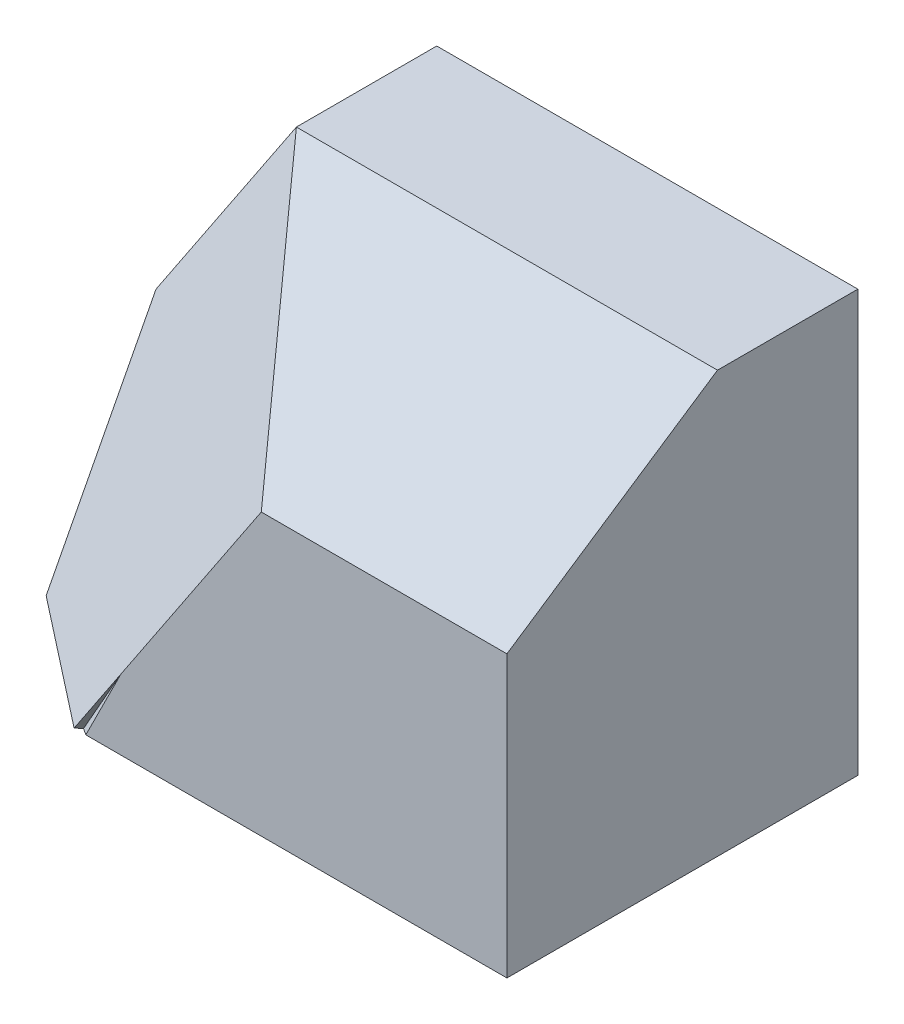
SolidWorks part; units mm, degrees
ref_plane "Front Plane" through (0, 0, 0) normal (0, 0, 1) x (1, 0, 0)
ref_plane "Top Plane" through (0, 0, 0) normal (0, 1, 0) x (1, 0, 0)
ref_plane "Right Plane" through (0, 0, 0) normal (1, 0, 0) x (0, 0, -1)
sketch "Sketch1" plane through (0, 0, 0) normal (0, 0, 1) x (1, 0, 0)
  line L1 (0, 0) -> (80, 0)
  line L2 (0, 0) -> (0, 60)
  line L3 (0, 60) -> (80, 60)
  line L4 (80, 0) -> (80, 60)
  dimension "D1" = 80
  dimension "D2" = 60
extrude "Boss-Extrude1" add sketch "Sketch1" along normal blind 50
sketch "Sketch2" plane through (0, 0, 50) normal (0, 0, 1) x (1, 0, 0)
  line L0 (0, 30) -> (20, 60)
  line L1 (0, 60) -> (0, 0) construction
  line L2 (80, 60) -> (0, 60) construction
  line L3 (20, 60) -> (0, 60)
  line L4 (0, 60) -> (0, 30)
  dimension "D1" = 20
  dimension "D2" = 30
extrude "Cut-Extrude1" cut sketch "Sketch2" against normal blind 50
sketch "Sketch3" plane through (80, 0, 0) normal (1, 0, 0) x (0, 0, -1)
  line L0 (-30, 60) -> (-50, 40)
  line L1 (-50, 60) -> (0, 60) construction
  line L2 (-50, 0) -> (-50, 60) construction
  line L3 (-50, 40) -> (-50, 60)
  line L4 (-50, 60) -> (-30, 60)
  dimension "D1" = 20
  dimension "D2" = 20
extrude "Cut-Extrude2" cut sketch "Sketch3" against normal blind 124
sketch "Sketch4" plane through (0, 0, 50) normal (0, 0, 1) x (1, 0, 0)
  line L0 (20, 0) -> (40, 40)
  line L3 (0, 0) -> (80, 0) construction
  line L4 (6.6667, 40) -> (80, 40) construction
  dimension "D1" = 20
  dimension "D2" = 40
sketch "Sketch5" plane through (-13.8462, 9.2308, 0) normal (-0.8321, 0.5547, 0) x (0, 0, 1)
ref_plane "Plane1" through (-15.7143, 7.8571, 23.5714) normal (-0.5345, 0.2673, 0.8018) x (0.8452, 0.169, 0.5071)
sketch "Sketch6" plane through (-15.7143, 7.8571, 23.5714) normal (-0.5345, 0.2673, 0.8018) x (0.8452, 0.169, 0.5071)
  line L0 (65.922, 22.1359) -> (42.2577, -15.8114)
  line L1 (42.2577, -15.8114) -> (42.2577, 47.4342)
  line L2 (42.2577, 47.4342) -> (65.922, 22.1359)
  line L3 (65.922, 22.1359) -> (65.7922, 21.6331)
extrude "Cut-Extrude3" cut sketch "Sketch6" along normal blind 124 contours L2 L1 L0
sketch "Sketch7" plane through (35.7143, 7.1429, 21.4286) normal (0.8452, 0.169, 0.5071) x (0.4972, 0.0994, -0.8619)
  line L0 (-33.1497, 36.8698) -> (-33.1497, -3.9223)
  line L1 (-33.1497, -3.9223) -> (-9.9449, 54.9125)
  line L2 (-9.9449, 54.9125) -> (-33.1497, 36.8698)
extrude "Cut-Extrude4" cut sketch "Sketch7" against normal blind 124
sketch "Sketch8" plane through (-16.4835, -3.2967, 28.5714) normal (0.4972, 0.0994, -0.8619) x (-0.8676, 0.057, -0.494)
  line L0 (-25.737, 43.8217) -> (-32.8299, 45.4676)
  line L1 (-32.8299, 45.4676) -> (-42.0506, 5.7312)
  line L2 (-42.0506, 5.7312) -> (-18.9988, 4.4086)
  line L3 (-18.9988, 4.4086) -> (-18.9988, 34.6077)
  line L4 (-18.9988, 34.6077) -> (-25.737, 43.8217)
extrude "Cut-Extrude5" cut sketch "Sketch8" against normal blind 124
sketch "Sketch9" plane through (-22.7513, 35.2646, 26.164) normal (0.46, -0.7131, -0.5291) x (0.8879, 0.3695, 0.2741)
  line L0 (32.2081, 14.0891) -> (39.1389, 16.321)
  line L1 (39.1389, 16.321) -> (48.149, -11.6579)
  line L2 (48.149, -11.6579) -> (32.2081, 14.0891)
extrude "Cut-Extrude6" cut sketch "Sketch9" against normal blind 124
sketch "Sketch10" plane through (-0.963, -2.4074, 2.4074) normal (0.2722, 0.6804, -0.6804) x (0.9623, -0.1925, 0.1925)
  line L0 (8.581, -63.6396) -> (7.0762, -60.1585)
  line L1 (7.0762, -60.1585) -> (13.4715, -63.6396)
  line L2 (13.4715, -63.6396) -> (8.581, -63.6396)
extrude "Cut-Extrude7" cut sketch "Sketch10" against normal blind 124
sketch "Sketch11" plane through (-15.3461, 7.9439, 1.8054) normal (0.8833, -0.4572, -0.1039) x (-0.0923, 0.0478, -0.9946)
  line L0 (-47.5106, 39.7118) -> (-44.7445, 37.1173)
  line L1 (-44.7445, 37.1173) -> (-48.4569, 37.4261)
  line L2 (-48.4569, 37.4261) -> (-48.4569, 38.7029)
  line L3 (-47.5106, 39.7118) -> (-48.4569, 38.7029)
extrude "Cut-Extrude8" cut sketch "Sketch11" against normal blind 124
sketch "Sketch12" plane through (-7.2308, 36.1538, 0) normal (0.1961, -0.9806, 0) x (0.9806, 0.1961, 0)
  line L0 (13.3359, 50) -> (13.83, 50)
  line L1 (13.83, 50) -> (13.3359, 46.3077)
  line L2 (13.3359, 46.3077) -> (13.3359, 50)
  line L3 (13.3359, 46.3077) -> (13.3359, 50) construction
extrude "Cut-Extrude9" cut sketch "Sketch12" against normal blind 124
sketch "Sketch14" plane through (0, 60, 0) normal (0, 1, 0) x (1, 0, 0)
  line L0 (20, -20) -> (80, -20)
  line L1 (20, 0) -> (20, -30) construction
  line L2 (80, -30) -> (80, 0) construction
  line L3 (20, -30) -> (80, -30) construction
  dimension "D1" = 10
ref_plane "Plane2" through (0, 50.7692, 33.8462) normal (0, -0.8321, -0.5547) x (-1, 0, 0)
sketch "Sketch15" plane through (0, 50.7692, 33.8462) normal (0, -0.8321, -0.5547) x (-1, 0, 0)
  line L0 (-20, 16.641) -> (-80, 16.641)
  line L1 (-80, 16.641) -> (-80, -19.4145)
  line L2 (-80, -19.4145) -> (-40, -19.4145)
  line L3 (-40, -19.4145) -> (-20, 16.641)
extrude "Cut-Extrude10" cut sketch "Sketch15" against normal blind 124
sketch "Sketch16" plane through (22.3529, 6.8778, -10.3167) normal (0.8745, 0.2691, -0.4036) x (-0.3858, -0.1187, -0.9149)
  line L0 (-44.0652, 50.1077) -> (-33.1354, 51.465)
  line L1 (-33.1354, 51.465) -> (-65.9247, 26.4677)
  line L2 (-65.9247, 26.4677) -> (-44.0652, 50.1077)
extrude "Cut-Extrude11" cut sketch "Sketch16" against normal blind 124
sketch "Sketch17" plane through (-13.4749, 53.1222, 6.2192) normal (0.2443, -0.9631, -0.1128) x (0.9697, 0.2426, 0.0284)
  line L0 (39.2805, 22.8198) -> (34.5209, 12.8876)
  line L1 (34.5209, 12.8876) -> (33.5672, 22.828)
  line L2 (33.5672, 22.828) -> (35.5831, 23.9626)
  line L3 (35.5831, 23.9626) -> (39.2805, 22.8198)
extrude "Cut-Extrude12" cut sketch "Sketch17" against normal blind 124
sketch "Sketch18" plane through (-13.8462, 9.2308, 0) normal (-0.8321, 0.5547, 0) x (0, 0, 1)
  line L0 (20, 61.017) -> (20, 24.9615)
  line L1 (0, 24.9615) -> (26.6667, 24.9615) construction
  line L2 (0, 24.9615) -> (0, 61.017) construction
sketch "Sketch21" plane through (0, 0, 50) normal (0, 0, 1) x (1, 0, 0)
  line L0 (18.3333, 0) -> (45, 40)
  line L1 (20, 0) -> (80, 0) construction
  line L2 (40, 40) -> (80, 40) construction
  line L3 (20, 60) -> (0, 30) construction
  dimension "D1" = 35
ref_plane "Plane4" through (-14.8044, 9.8696, 18.9168) normal (-0.5701, 0.38, 0.7284) x (0.8216, 0.2637, 0.5054)
sketch "Sketch22" plane through (-14.8044, 9.8696, 18.9168) normal (-0.5701, 0.38, 0.7284) x (0.8216, 0.2637, 0.5054)
  line L0 (42.3618, 43.9438) -> (72.7903, 12.3351)
  line L1 (72.7903, 12.3351) -> (40.3332, -23.1283)
  line L2 (40.3332, -23.1283) -> (18.019, 17.3462)
  line L3 (18.019, 17.3462) -> (42.3618, 43.9438)
extrude "Cut-Extrude14" cut sketch "Sketch22" along normal blind 124
sketch "Sketch23" plane through (17.3792, 15.9171, 5.2965) normal (0.7195, 0.659, 0.2193) x (0.1617, 0.1481, -0.9757)
  line L0 (-15.0703, 22.1234) -> (-22.7557, 20.2833)
  line L1 (-22.7557, 20.2833) -> (-41.426, -7.4531)
  line L2 (-41.426, -7.4531) -> (-15.0703, 22.1234)
extrude "Cut-Extrude15" cut sketch "Sketch23" against normal blind 124
sketch "Sketch24" plane through (-14.8044, 9.8696, 18.9168) normal (-0.5701, 0.38, 0.7284) x (0.8216, 0.2637, 0.5054)
  line L0 (42.3618, 43.9438) -> (18.019, 17.3462)
  line L1 (18.019, 17.3462) -> (18.019, -16.4915)
  line L2 (42.3618, 43.9438) -> (72.7903, 12.3351)
  line L3 (72.7903, 12.3351) -> (41.7026, -23.1283)
  line L4 (41.7026, -23.1283) -> (18.019, -16.4915)
ref_plane "Plane5" through (-14.8044, 9.8696, 18.9168) normal (-0.5701, 0.38, 0.7284) x (0.8216, 0.2637, 0.5054)
sketch "Sketch26" plane through (-14.8044, 9.8696, 18.9168) normal (-0.5701, 0.38, 0.7284) x (0.8216, 0.2637, 0.5054)
  line L0 (18.019, -16.4915) -> (40.3332, -23.1283)
  line L1 (40.3332, -23.1283) -> (72.7903, 12.3351)
  line L2 (72.7903, 12.3351) -> (42.3618, 43.9438)
  line L3 (42.3618, 43.9438) -> (18.019, 17.3462)
  line L4 (18.019, 17.3462) -> (18.019, -16.4915)
extrude "Boss-Extrude2" add sketch "Sketch26" against normal blind 5
sketch "Sketch27" plane through (0, 0, 0) normal (0, -1, 0) x (1, 0, 0)
  line L1 (80, 0) -> (0, 0)
  line L2 (80, 0) -> (80, 50)
  line L3 (80, 50) -> (0, 50)
  line L4 (0, 0) -> (0, 50)
  dimension "D1" = 0
  dimension "D2" = 80
extrude "Cut-Extrude20" cut sketch "Sketch27" along normal blind 37
